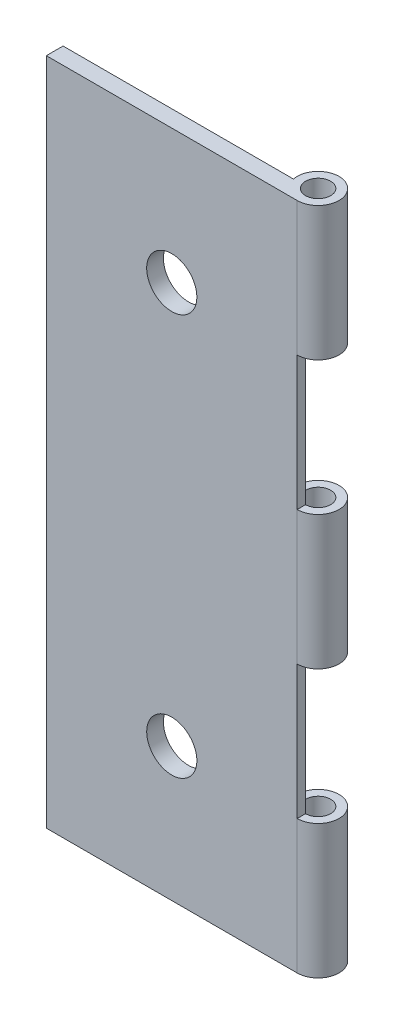
SolidWorks part; units mm, degrees
material "Stainless Steel (ferritic)"
ref_plane "Front Plane" through (0, 0, 0) normal (0, 0, 1) x (1, 0, 0)
ref_plane "Top Plane" through (0, 0, 0) normal (0, 1, 0) x (1, 0, 0)
ref_plane "Right Plane" through (0, 0, 0) normal (1, 0, 0) x (0, 0, -1)
sketch "Sketch1" plane through (0, 0, 0) normal (0, 0, 1) x (1, 0, 0)
  line L0 (-7.5, 0) -> (7.5, 0) construction
  line L1 (-7.5, -20) -> (7.5, -20)
  line L2 (-7.5, -20) -> (-7.5, 20)
  line L3 (-7.5, 20) -> (7.5, 20)
  line L4 (7.5, -20) -> (7.5, 20)
  line L5 (-7.5, -20) -> (7.5, 20) construction
  line L6 (-7.5, 20) -> (7.5, -20) construction
  circle A0 centre (0, 12) radius 1.5
  circle A1 centre (0, -12) radius 1.5
  point P0 (0, 0)
  dimension "D3" = 3
  dimension "D1" = 15
  dimension "D2" = 40
  dimension "D4" = 8
extrude "Boss-Extrude2" add sketch "Sketch1" along normal blind 1
sketch "Sketch2" plane through (0, 20, 0) normal (0, 1, 0) x (1, 0, 0)
  line L0 (7.5, -1) -> (9.3423, -1) construction
  line L1 (7.5, -1) -> (7.5, 0) construction
  circle A0 centre (7.5, 0.25) radius 1.25
  dimension "D1" = 2.5
  dimension "D2" = 1.25
  dimension "D3" = 0
extrude "Boss-Extrude3" add sketch "Sketch2" against normal blind 8
sketch "Sketch3" plane through (0, 20, 0) normal (0, 1, 0) x (1, 0, 0)
  circle A0 centre (7.5, 0.25) radius 0.75
  dimension "D1" = 1.5
extrude "Cut-Extrude1" cut sketch "Sketch3" against normal blind 40
pattern_linear "LPattern1" count 3 spacing 16 along (0, -1, 0) of "Boss-Extrude3"
sketch "Sketch4" plane through (0, 20, 0) normal (0, 1, 0) x (1, 0, 0)
  circle A0 centre (7.5, 0.25) radius 0.75
  dimension "D1" = 1.5
extrude "Cut-Extrude2" cut sketch "Sketch4" against normal blind 40
